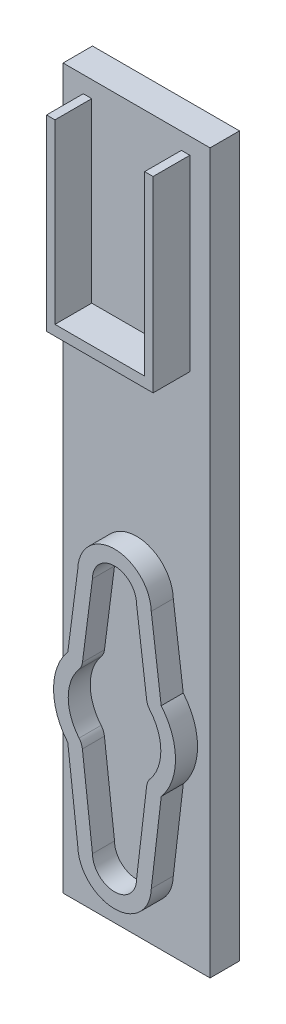
SolidWorks part; units mm, degrees
ref_plane "Front Plane" through (0, 0, 0) normal (0, 0, 1) x (1, 0, 0)
ref_plane "Top Plane" through (0, 0, 0) normal (0, 1, 0) x (1, 0, 0)
ref_plane "Right Plane" through (0, 0, 0) normal (1, 0, 0) x (0, 0, -1)
sketch "Sketch1" plane through (0, 0, 0) normal (0, 0, 1) x (1, 0, 0)
  line L0 (-6.3497, 5.3452) -> (-4.9979, 15.7883)
  line L1 (4.9979, 15.7883) -> (6.3497, 5.3452)
  line L2 (6.3584, -5.3348) -> (4.9983, -16.8891)
  line L3 (-4.9983, -16.8891) -> (-6.3584, -5.3348)
  line L7 (-4.3663, 5.0884) -> (-3, 15.6431)
  line L12 (-4.4473, -5.576) -> (-4.3316, -5.4454) construction
  line L13 (4.3316, -5.4454) -> (4.4473, -5.576) construction
  line L15 (3, 15.6431) -> (4.3663, 5.0884)
  line L16 (4.3721, -5.101) -> (3, -16.7569)
  line L18 (-3, -16.7569) -> (-4.3721, -5.101)
  arc A0 (-4.8197, 4.0572) -> (-4.8263, -4.0493) centre (0, 0) ccw
  arc A2 (3, 15.6431) -> (-3, 15.6431) centre (0, 15.6431) ccw
  arc A3 (-3, -16.7569) -> (3, -16.7569) centre (0, -16.7569) ccw
  arc A4 (4.8263, -4.0493) -> (4.8197, 4.0572) centre (0, 0) ccw
  arc A5 (-4.3721, -5.101) -> (-4.8263, -4.0493) centre (-6.3584, -5.3348) ccw
  arc A6 (4.8263, -4.0493) -> (4.3721, -5.101) centre (6.3584, -5.3348) ccw
  arc A7 (4.8197, 4.0572) -> (4.3663, 5.0884) centre (6.3497, 5.3452) cw
  arc A8 (-4.3663, 5.0884) -> (-4.8197, 4.0572) centre (-6.3497, 5.3452) cw
  arc A9 (4.9979, 15.7883) -> (-4.9979, 15.7883) centre (0, 15.6431) ccw
  arc A10 (6.3497, 5.3452) -> (6.3497, 5.3452) centre (6.3497, 5.3452) cw
  arc A11 (6.3584, -5.3348) -> (6.3497, 5.3452) centre (0, 0) ccw
  arc A12 (6.3584, -5.3348) -> (6.3584, -5.3348) centre (6.3584, -5.3348) ccw
  arc A13 (-4.9983, -16.8891) -> (4.9983, -16.8891) centre (0, -16.7569) ccw
  arc A14 (-6.3584, -5.3348) -> (-6.3584, -5.3348) centre (-6.3584, -5.3348) ccw
  arc A15 (-6.3497, 5.3452) -> (-6.3584, -5.3348) centre (0, 0) ccw
  arc A16 (-6.3497, 5.3452) -> (-6.3497, 5.3452) centre (-6.3497, 5.3452) cw
  dimension "D1" = 2
  dimension "D2" = 2
extrude "Boss-Extrude1" add sketch "Sketch1" along normal blind 3
sketch "Sketch2" plane through (0, 0, 0) normal (0, 0, -1) x (-1, 0, 0)
  line L1 (10, -26.4095) -> (-10, -26.4095)
  line L2 (10, -26.4095) -> (10, 26.4095)
  line L4 (-10, -26.4095) -> (-10, 26.4095)
  line L5 (10, -26.4095) -> (-10, 26.4095) construction
  line L6 (10, 26.4095) -> (-10, -26.4095) construction
  line L8 (-10, 26.4095) -> (-10, 71.4095)
  line L9 (-10, 71.4095) -> (10, 71.4095)
  line L10 (10, 26.4095) -> (10, 71.4095)
  point P0 (0, 0)
  dimension "D1" = 20
  dimension "D2" = 45
extrude "Boss-Extrude2" add sketch "Sketch2" along normal blind 4 contours L8 L9 L10 L2 L1 L4
sketch "Sketch3" plane through (0, 0, 0) normal (0, 0, 1) x (1, 0, 0)
  line L0 (0, 71.4095) -> (0, 56.4095)
  line L1 (10, 71.4095) -> (-10, 71.4095) construction
  line L2 (-6.1, 67.7595) -> (-6.1, 69.1595)
  line L3 (6.1, 45.0595) -> (-6.1, 45.0595)
  line L4 (6.1, 45.0595) -> (6.1, 67.7595)
  line L5 (6.1, 67.7595) -> (-6.1, 67.7595)
  line L6 (-6.1, 45.0595) -> (-6.1, 67.7595)
  line L7 (6.1, 45.0595) -> (-6.1, 67.7595) construction
  line L8 (6.1, 67.7595) -> (-6.1, 45.0595) construction
  line L9 (7.25, 43.6595) -> (-7.25, 43.6595)
  line L10 (7.25, 43.6595) -> (7.25, 69.1595)
  line L11 (7.25, 69.1595) -> (-7.25, 69.1595)
  line L12 (-7.25, 43.6595) -> (-7.25, 69.1595)
  line L13 (7.25, 43.6595) -> (-7.25, 69.1595) construction
  line L14 (7.25, 69.1595) -> (-7.25, 43.6595) construction
  line L15 (6.1, 67.7595) -> (6.1, 69.1595)
  dimension "D1" = 15
  dimension "D2" = 22.7
  dimension "D3" = 12.2
  dimension "D4" = 14.5
  dimension "D5" = 25.5
extrude "Boss-Extrude3" add sketch "Sketch3" along normal blind 5 contours L15 L4 L3 L6 L2 L11 L12 L9 L10
